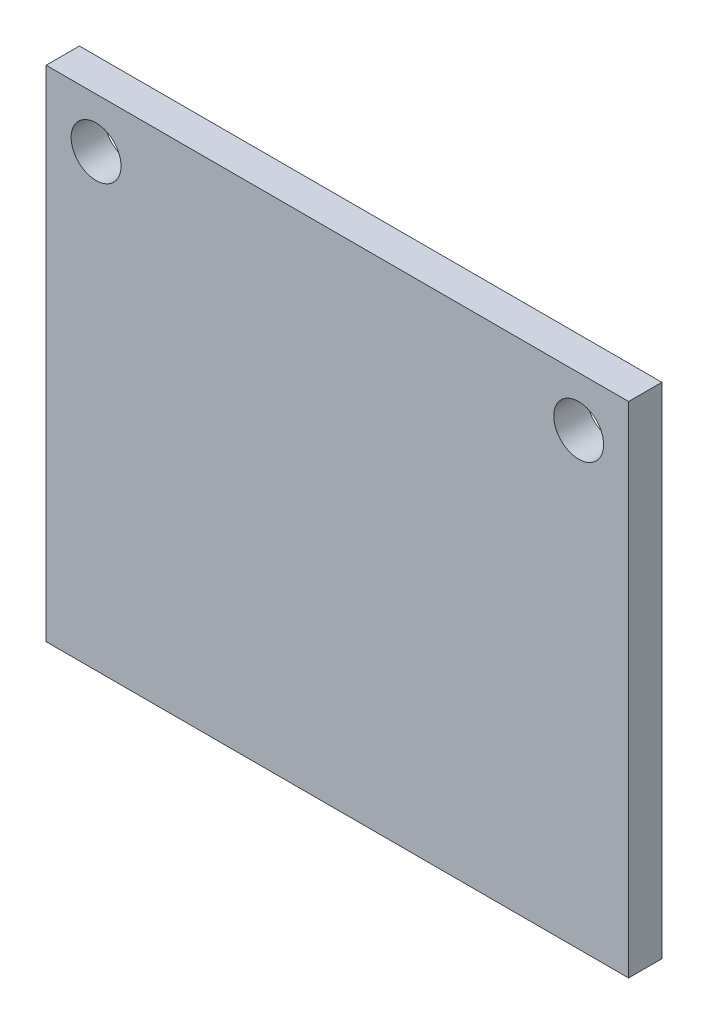
SolidWorks part; units mm, degrees
ref_plane "Front Plane" through (0, 0, 0) normal (0, 0, 1) x (1, 0, 0)
ref_plane "Top Plane" through (0, 0, 0) normal (0, 1, 0) x (1, 0, 0)
ref_plane "Right Plane" through (0, 0, 0) normal (1, 0, 0) x (0, 0, -1)
sketch "Sketch1" plane through (0, 0, 0) normal (0, 0, 1) x (1, 0, 0)
  line L1 (-13.1997, 8.0631) -> (21.8003, 8.0631)
  line L2 (-13.1997, 8.0631) -> (-13.1997, -21.9369)
  line L3 (-13.1997, -21.9369) -> (21.8003, -21.9369)
  line L4 (21.8003, 8.0631) -> (21.8003, -21.9369)
  dimension "D1" = 35
  dimension "D2" = 30
extrude "Boss-Extrude1" add sketch "Sketch1" along normal blind 2
sketch "Sketch2" plane through (0, 0, 2) normal (0, 0, 1) x (1, 0, 0)
  line L0 (21.8003, 8.0631) -> (-13.1997, 8.0631) construction
  line L1 (-13.1997, 8.0631) -> (-13.1997, -21.9369) construction
  line L2 (21.8003, -21.9369) -> (21.8003, 8.0631) construction
  circle A0 centre (-10.1997, 5.0631) radius 1.5
  circle A1 centre (18.8003, 5.0631) radius 1.5
  dimension "D2" = 3
  dimension "D6" = 3
  dimension "D1" = 3
  dimension "D3" = 3
  dimension "D4" = 3
  dimension "D5" = 3
extrude "Cut-Extrude1" cut sketch "Sketch2" against normal blind 2
